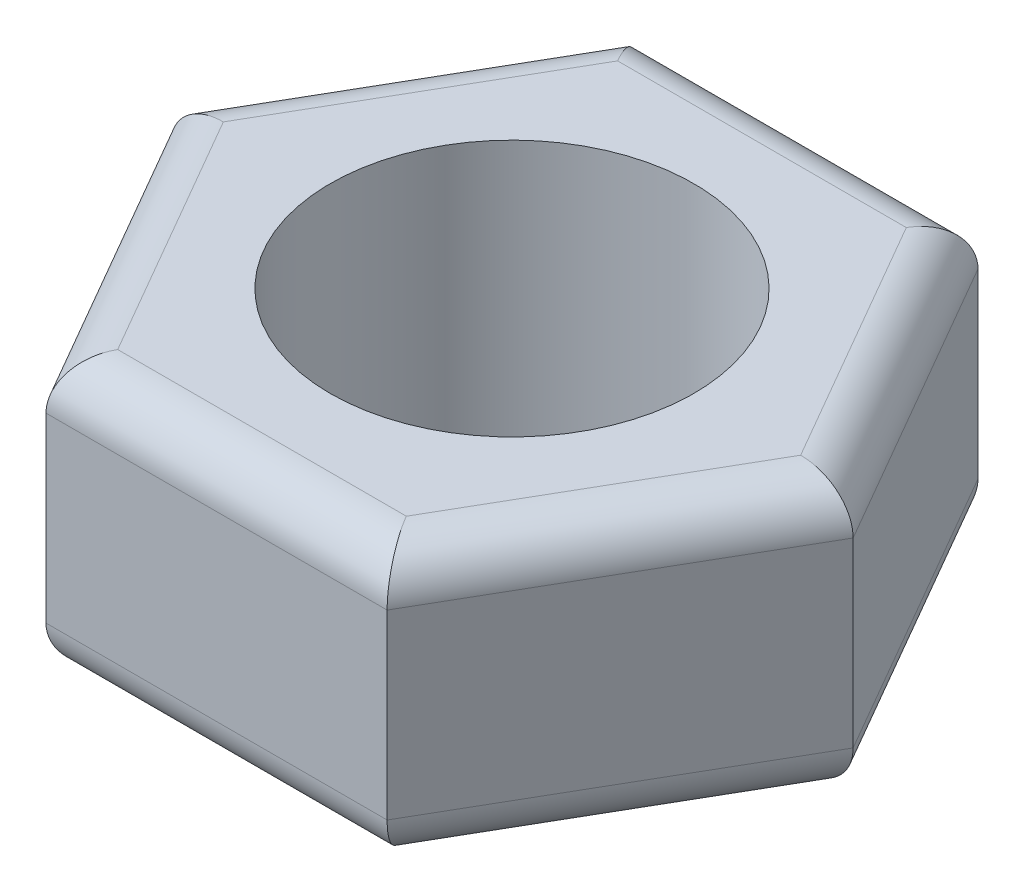
SolidWorks part; units mm, degrees
ref_plane "Front Plane" through (0, 0, 0) normal (0, 0, 1) x (1, 0, 0)
ref_plane "Top Plane" through (0, 0, 0) normal (0, 1, 0) x (1, 0, 0)
ref_plane "Right Plane" through (0, 0, 0) normal (1, 0, 0) x (0, 0, -1)
sketch "Sketch1" plane through (0, 0, 0) normal (0, 1, 0) x (1, 0, 0)
  line L1 (7.5056, 0) -> (3.7528, 6.5)
  line L2 (3.7528, 6.5) -> (-3.7528, 6.5)
  line L3 (-3.7528, 6.5) -> (-7.5056, 0)
  line L4 (-7.5056, 0) -> (-3.7528, -6.5)
  line L5 (-3.7528, -6.5) -> (3.7528, -6.5)
  line L6 (3.7528, -6.5) -> (7.5056, 0)
  circle A0 centre (0, 0) radius 6.5 construction
  circle A1 centre (0, 0) radius 4
  dimension "D1" = 8
  dimension "D2" = 13
extrude "Boss-Extrude1" add sketch "Sketch1" along normal blind 6
fillet "Fillet1" radius 1 12 edges at (5.6292, 0, -3.25) (0, 0, -6.5) (-5.6292, 0, -3.25) (-5.6292, 0, 3.25) (0, 0, 6.5) (5.6292, 0, 3.25) (0, 6, 6.5) (-5.6292, 6, 3.25) (-5.6292, 6, -3.25) (0, 6, -6.5) (5.6292, 6, -3.25) (5.6292, 6, 3.25)
